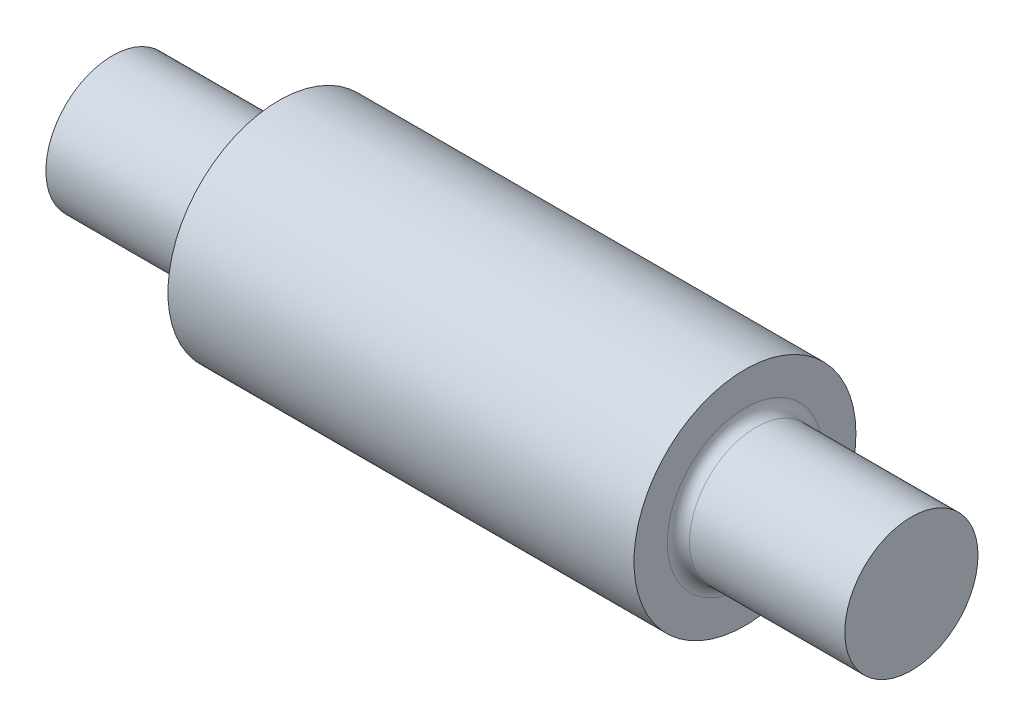
SolidWorks part; units mm, degrees
material "Brass"
ref_plane "Front Plane" through (0, 0, 0) normal (0, 0, 1) x (1, 0, 0)
ref_plane "Top Plane" through (0, 0, 0) normal (0, 1, 0) x (1, 0, 0)
ref_plane "Right Plane" through (0, 0, 0) normal (1, 0, 0) x (0, 0, -1)
sketch "Sketch1" plane through (0, 0, 0) normal (1, 0, 0) x (0, 0, -1)
  circle A0 centre (0, 0) radius 10
  dimension "D1" = 20
extrude "Boss-Extrude1" add sketch "Sketch1" along normal mid plane 42
sketch "草图1" plane through (21, 0, 0) normal (1, 0, 0) x (0, 0, -1)
  circle A0 centre (0, 0) radius 6
extrude "凸台-拉伸1" add sketch "草图1" along normal blind 15
mirror "镜向1" about plane through (0, 0, 0) normal (1, 0, 0) of "凸台-拉伸1"
fillet "圆角1" radius 1 2 edges at (-21, 0, -6) (21, 0, -6)
